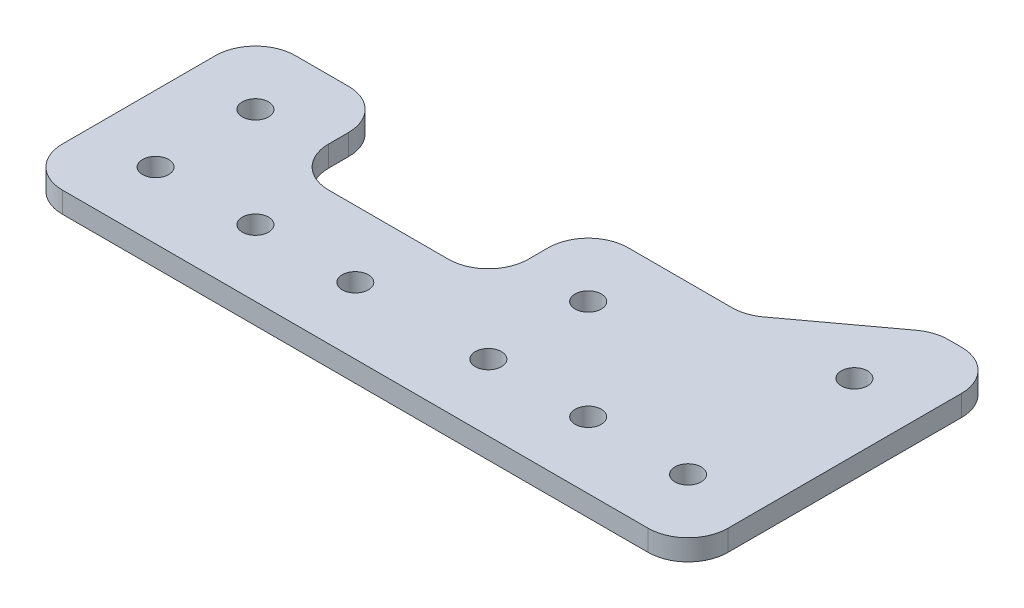
SolidWorks part; units mm, degrees
material "ABS"
ref_plane "Front Plane" through (0, 0, 0) normal (0, 0, 1) x (1, 0, 0)
ref_plane "Top Plane" through (0, 0, 0) normal (0, 1, 0) x (1, 0, 0)
ref_plane "Right Plane" through (0, 0, 0) normal (1, 0, 0) x (0, 0, -1)
sketch "Sketch1" plane through (0, 25.4, 0) normal (0, 1, 0) x (1, 0, 0)
  line L0 (-165.1, 152.4) -> (-190.5, 152.4) construction
  line L1 (-190.5, 152.4) -> (-190.5, -279.4) construction
  line L2 (-127, -260.35) -> (-97.0359, -260.35)
  line L3 (-165.1, -279.4) -> (-165.1, 152.4) construction
  line L4 (-101.6, 152.4) -> (-127, 152.4) construction
  line L5 (-127, 152.4) -> (-127, -279.4) construction
  line L6 (-97.0359, -260.35) -> (-76.2, -244.9841)
  line L8 (-190.5, -279.4) -> (-190.5, -304.8) construction
  line L9 (-190.5, -304.8) -> (190.5, -304.8) construction
  line L10 (190.5, -304.8) -> (190.5, -279.4) construction
  line L12 (-165.1, 152.4) -> (-190.5, 152.4)
  line L13 (-190.5, -260.35) -> (-190.5, -279.4)
  line L14 (-76.2, -244.9841) -> (-63.5, -244.9841)
  line L15 (-165.1, -279.4) -> (-165.1, -260.35)
  line L16 (-101.6, 152.4) -> (-127, 152.4)
  line L17 (-127, -260.35) -> (-127, -279.4)
  line L18 (-63.5, -292.1) -> (-190.5, -292.1) construction
  line L20 (-190.5, -279.4) -> (-190.5, -304.8)
  line L21 (-190.5, -304.8) -> (-63.5, -304.8)
  line L22 (190.5, -304.8) -> (190.5, -279.4)
  line L24 (-63.5, -304.8) -> (-63.5, -244.9841)
  line L26 (-127, -279.4) -> (-165.1, -279.4)
  line L27 (-177.8, -260.35) -> (-177.8, -304.8) construction
  line L28 (-114.3, -260.35) -> (-114.3, -304.8) construction
  line L29 (-190.5, -260.35) -> (-165.1, -260.35)
  circle A0 centre (-114.3, -292.1) radius 2.5
  circle A1 centre (-177.8, -292.1) radius 2.5
  circle A2 centre (-158.75, -292.1) radius 2.5
  circle A3 centre (-95.25, -292.1) radius 2.5
  circle A4 centre (-139.7, -292.1) radius 2.5
  circle A5 centre (-76.2, -292.1) radius 2.5
  circle A6 centre (-114.3, -273.05) radius 2.5
  circle A7 centre (-177.8, -273.05) radius 2.5
  circle A8 centre (-76.2, -260.35) radius 2.5
  arc A10 (-177.8, -251.5) -> (-177.8, -256.5) centre (-177.8, -254) ccw [skipped]
  arc A11 (-114.3, -256.5) -> (-114.3, -251.5) centre (-114.3, -254) ccw [skipped]
  dimension "D3" = 5
  dimension "D1" = 127
  dimension "D2" = 2
  dimension "D6" = 12.7
  dimension "D4" = 3
  dimension "D5" = 3
extrude "Boss-Extrude1" add sketch "Sketch1" along normal blind 4
fillet "Fillet1" radius 7.62 10 edges at (-63.5, 27.4, 304.8) (-190.5, 27.4, 304.8) (-190.5, 27.4, 260.35) (-165.1, 27.4, 260.35) (-127, 27.4, 260.35) (-165.1, 27.4, 279.4) (-127, 27.4, 279.4) (-76.2, 27.4, 244.9841) (-63.5, 27.4, 244.9841) (-97.0359, 27.4, 260.35)
